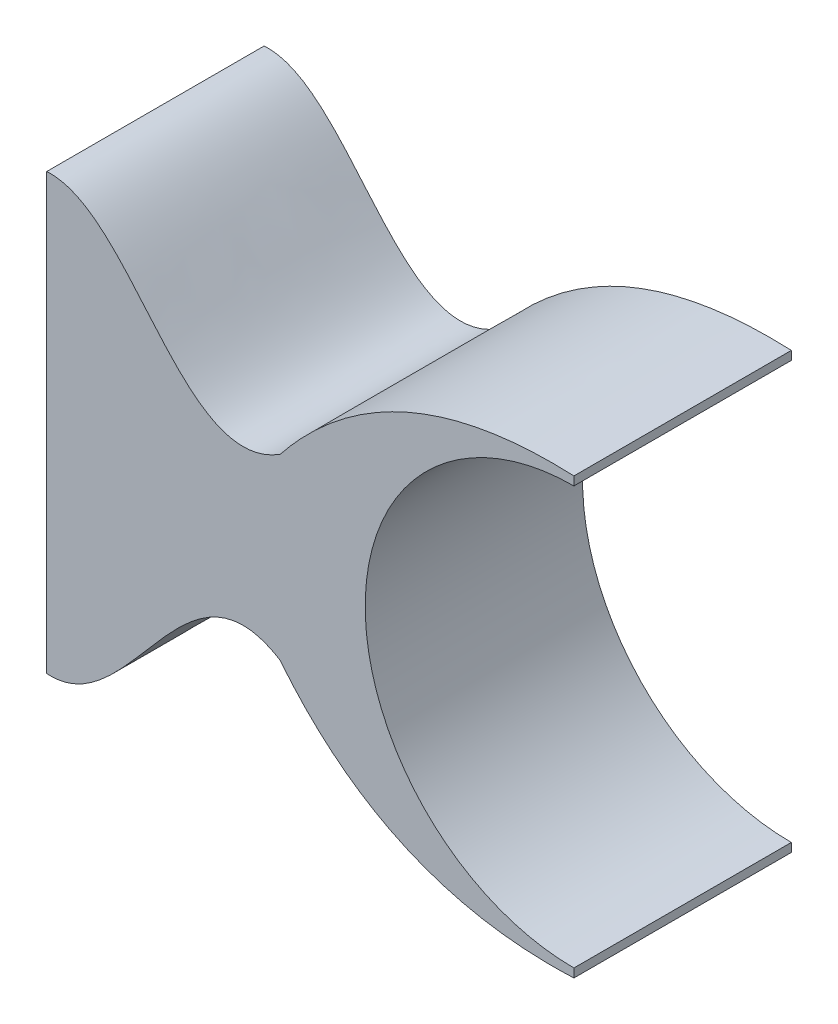
SolidWorks part; units mm, degrees
ref_plane "Front Plane" through (0, 0, 0) normal (0, 0, 1) x (1, 0, 0)
ref_plane "Top Plane" through (0, 0, 0) normal (0, 1, 0) x (1, 0, 0)
ref_plane "Right Plane" through (0, 0, 0) normal (1, 0, 0) x (0, 0, -1)
sketch "Sketch1" plane through (0, 0, 0) normal (0, 0, 1) x (1, 0, 0)
  line L0 (0, 0) -> (-9.9188, 0) construction
  line L1 (-6.0626, 2.5) -> (-6.0626, -2.5)
  line L2 (0, 2.5) -> (0, 2.4)
  line L3 (0, -2.5) -> (0, -2.4)
  arc A1 (0, 2.4) -> (0, -2.4) centre (0, 0) ccw
  spline S0 degree 2 poles (0, 2.5) (-2.1284, 2.5961) (-3.3783, 1.0256) knots 0 0 0 1 1 1
  spline S1 degree 3 poles (-3.3783, 1.0256) (-4.4922, 0.3252) (-5.0825, 2.5685) (-6.0626, 2.5) knots 0 0 0 0 1 1 1 1
  spline S2 degree 3 poles (-3.3783, -1.0256) (-4.4922, -0.3252) (-5.0825, -2.5685) (-6.0626, -2.5) knots 0 0 0 0 1 1 1 1
  spline S3 degree 2 poles (0, -2.5) (-2.1284, -2.5961) (-3.3783, -1.0256) knots 0 0 0 1 1 1
  dimension "D2" = 4.8
extrude "Boss-Extrude1" add sketch "Sketch1" along normal blind 2.5
